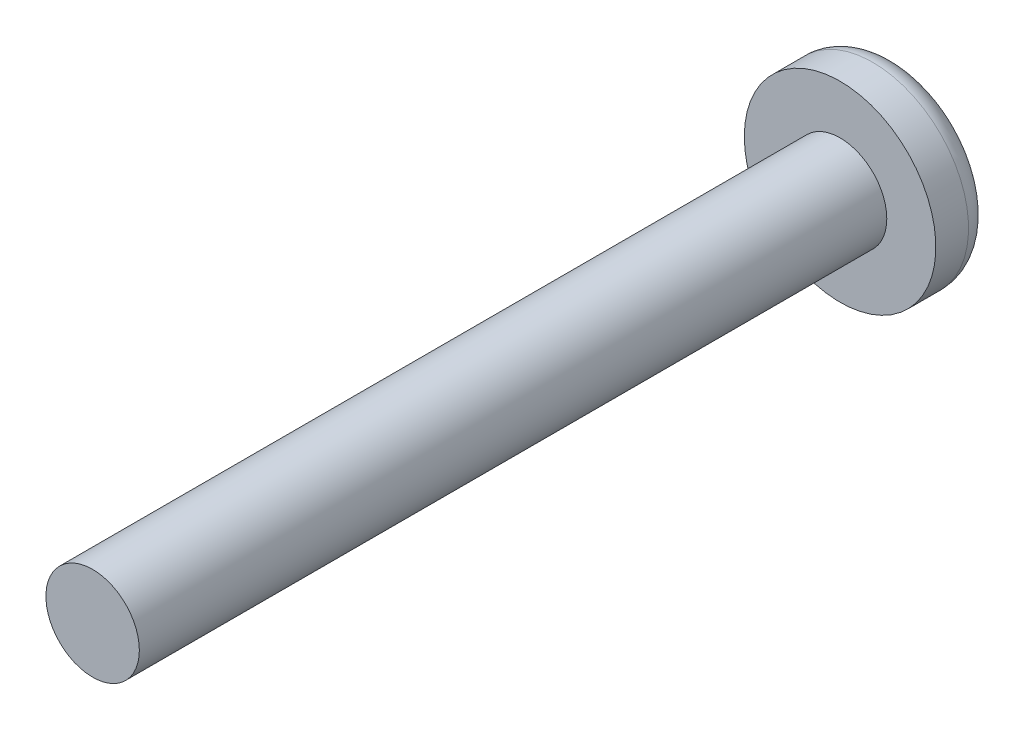
SolidWorks part; units mm, degrees
ref_plane "Piano frontale" through (0, 0, 0) normal (0, 0, 1) x (1, 0, 0)
ref_plane "Piano superiore" through (0, 0, 0) normal (0, 1, 0) x (1, 0, 0)
ref_plane "Piano destro" through (0, 0, 0) normal (1, 0, 0) x (0, 0, -1)
sketch "Schizzo1" plane through (0, 0, 0) normal (0, 0, 1) x (1, 0, 0)
  circle A0 centre (0, 0) radius 1
  dimension "D1" = 2
extrude "Estrusione-Estrusione1" add sketch "Schizzo1" along normal blind 16
sketch "Schizzo2" plane through (0, 0, 0) normal (0, 0, -1) x (-1, 0, 0)
  circle A0 centre (0, 0) radius 2.05
  dimension "D1" = 4.1
extrude "Estrusione-Estrusione2" add sketch "Schizzo2" along normal blind 1.2
fillet "Raccordo1" radius 0.5 1 edges at (-2.05, 0, -1.2)
sketch "Schizzo3" plane through (0, 0, -1.2) normal (0, 0, -1) x (-1, 0, 0)
  line L0 (0, 2.4562) -> (0, -3.0328) construction
  line L1 (-2.6308, 0) -> (3.8082, 0) construction
  line L2 (-0.25, 0.25) -> (-1, 0.25)
  line L7 (-0.25, 0.25) -> (-0.25, 1)
  line L8 (-0.25, 1) -> (0.25, 1)
  line L9 (-1, 0.25) -> (-1, -0.25)
  line L12 (1, 0.25) -> (1, -0.25)
  line L13 (0.25, 0.25) -> (0.25, 1)
  line L14 (0.25, 0.25) -> (1, 0.25)
  line L15 (0.25, -0.25) -> (1, -0.25)
  line L16 (0.25, -0.25) -> (0.25, -1)
  line L17 (-0.25, -1) -> (0.25, -1)
  line L18 (-0.25, -0.25) -> (-0.25, -1)
  line L19 (-0.25, -0.25) -> (-1, -0.25)
  dimension "D1" = 2
  dimension "D3" = 0.25
  dimension "D4" = 1
  dimension "0.25" = 0.25
extrude "Taglio-Estrusione1" cut sketch "Schizzo3" against normal blind 0.5
